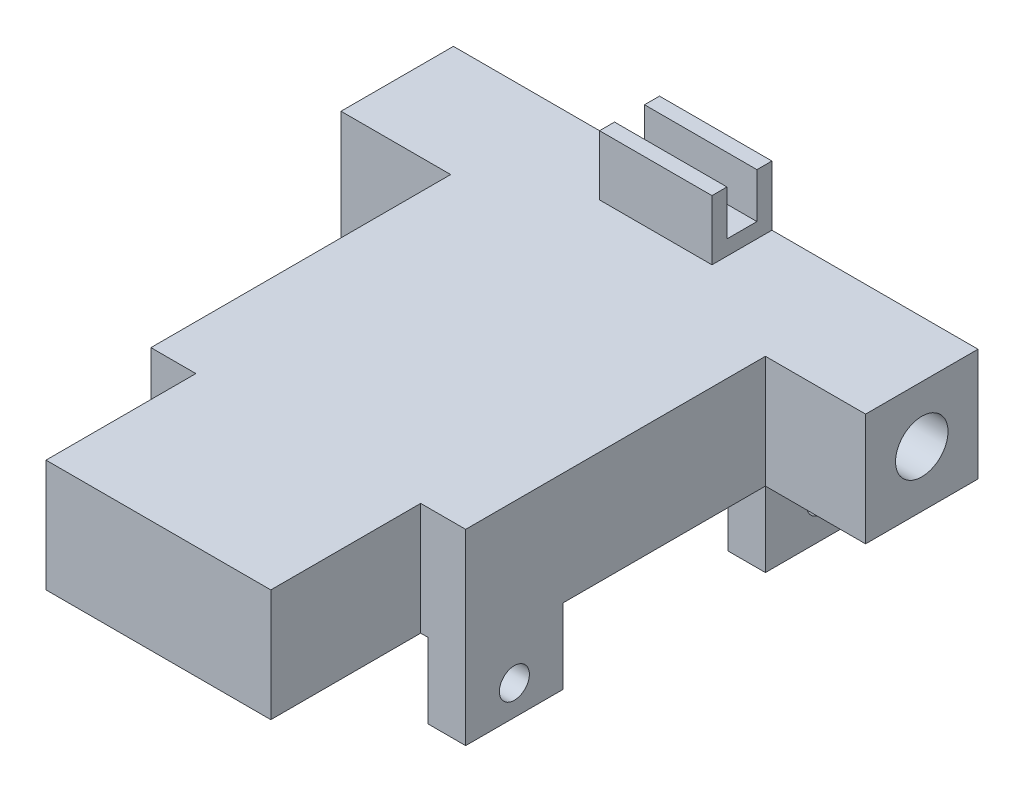
SolidWorks part; units mm, degrees
material "ABS"
ref_plane "Front Plane" through (0, 0, 0) normal (0, 0, 1) x (1, 0, 0)
ref_plane "Top Plane" through (0, 0, 0) normal (0, 1, 0) x (1, 0, 0)
ref_plane "Right Plane" through (0, 0, 0) normal (1, 0, 0) x (0, 0, -1)
sketch "Sketch1" plane through (0, 0, 0) normal (0, 0, 1) x (1, 0, 0)
  line L1 (0, 0) -> (88.9, 0)
  line L2 (0, 0) -> (0, -19.05)
  line L3 (0, -19.05) -> (88.9, -19.05)
  line L4 (88.9, 0) -> (88.9, -19.05)
  dimension "D1" = 88.9
  dimension "D2" = 19.05
extrude "Boss-Extrude1" add sketch "Sketch1" along normal blind 19.05
sketch "Sketch2" plane through (0, -19.05, 0) normal (0, -1, 0) x (1, 0, 0)
  line L0 (0, 19.05) -> (88.9, 19.05) construction
  line L1 (18.5839, 19.05) -> (24.9339, 19.05)
  line L2 (18.5839, 19.05) -> (18.5839, 0)
  line L3 (18.5839, 0) -> (24.9339, 0)
  line L4 (24.9339, 19.05) -> (24.9339, 0)
  line L5 (0, 0) -> (88.9, 0) construction
  line L7 (65.5739, 19.05) -> (71.9239, 19.05)
  line L8 (65.5739, 19.05) -> (65.5739, 0)
  line L9 (65.5739, 0) -> (71.9239, 0)
  line L10 (71.9239, 19.05) -> (71.9239, 0)
  point P12 (44.45, 0)
  dimension "D1" = 6.35
  dimension "D2" = 6.35
  dimension "D3" = 40.64
  dimension "D4" = 19.5161
extrude "Boss-Extrude2" add sketch "Sketch2" along normal blind 12.7
sketch "Sketch3" plane through (0, 0, 0) normal (-1, 0, 0) x (0, 0, 1)
  line L0 (0, 0) -> (0, -19.05) construction
  line L2 (19.05, -19.05) -> (0, -19.05) construction
  circle A0 centre (9.525, -9.525) radius 4.445
  dimension "D1" = 8.89
  dimension "D2" = 9.525
  dimension "D3" = 9.525
extrude "Cut-Extrude1" cut sketch "Sketch3" against normal blind 96.266
sketch "Sketch4" plane through (18.5839, 0, 0) normal (-1, 0, 0) x (0, 0, 1)
  line L0 (0, -31.75) -> (0, -19.05) construction
  line L1 (19.05, -31.75) -> (0, -31.75) construction
  circle A0 centre (9.525, -25.4) radius 2.54
  dimension "D1" = 5.08
  dimension "D2" = 9.525
  dimension "D3" = 6.35
extrude "Cut-Extrude2" cut sketch "Sketch4" against normal blind 96.266
sketch "Sketch5" plane through (0, 0, 19.05) normal (0, 0, 1) x (1, 0, 0)
  line L0 (88.9, 0) -> (0, 0) construction
  line L1 (18.5839, 0) -> (71.9239, 0)
  line L2 (18.5839, 0) -> (18.5839, -19.05)
  line L3 (18.5839, -19.05) -> (71.9239, -19.05)
  line L4 (71.9239, 0) -> (71.9239, -19.05)
  line L5 (71.9239, -19.05) -> (88.9, -19.05) construction
  line L6 (24.9339, -31.75) -> (24.9339, -19.05) construction
  dimension "D1" = 53.34
  dimension "D2" = 6.35
extrude "Boss-Extrude3" add sketch "Sketch5" along normal blind 50.8
sketch "Sketch6" plane through (0, -19.05, 0) normal (0, -1, 0) x (1, 0, 0)
  line L1 (18.5839, 69.85) -> (24.9339, 69.85)
  line L2 (18.5839, 69.85) -> (18.5839, 53.34)
  line L3 (18.5839, 53.34) -> (24.9339, 53.34)
  line L4 (24.9339, 69.85) -> (24.9339, 53.34)
  line L5 (71.9239, 69.85) -> (65.5739, 69.85)
  line L6 (71.9239, 69.85) -> (71.9239, 53.34)
  line L7 (71.9239, 53.34) -> (65.5739, 53.34)
  line L8 (65.5739, 69.85) -> (65.5739, 53.34)
  line L9 (18.5839, 69.85) -> (71.9239, 69.85) construction
  dimension "D1" = 6.35
  dimension "D2" = 6.35
  dimension "D3" = 16.51
  dimension "D4" = 16.51
extrude "Boss-Extrude4" add sketch "Sketch6" along normal blind 12.7
sketch "Sketch7" plane through (18.5839, 0, 0) normal (-1, 0, 0) x (0, 0, 1)
  line L0 (69.85, -31.75) -> (53.34, -31.75) construction
  line L1 (53.34, -31.75) -> (53.34, -19.05) construction
  circle A0 centre (61.595, -26.67) radius 2.54
  dimension "D1" = 5.08
  dimension "D2" = 5.08
  dimension "D3" = 8.255
extrude "Cut-Extrude3" cut sketch "Sketch7" against normal blind 61.976
sketch "Sketch8" plane through (0, 0, 0) normal (0, 1, 0) x (1, 0, 0)
  line L0 (88.9, 0) -> (0, 0) construction
  line L1 (34.925, 0) -> (53.975, 0)
  line L2 (34.925, 0) -> (34.925, -10.16)
  line L3 (34.925, -10.16) -> (53.975, -10.16)
  line L4 (53.975, 0) -> (53.975, -10.16)
  line L7 (88.9, 0) -> (0, 0)
  point P6 (44.45, 0)
  point P9 (44.45, 0)
  line M7 (88.9, 0) -> (0, 0)
  dimension "D1" = 19.05
  dimension "D2" = 10.16
extrude "Boss-Extrude5" add sketch "Sketch8" along normal blind 2.54 contours L4 L2 L3 M7
sketch "Sketch9" plane through (0, 2.54, 0) normal (0, 1, 0) x (1, 0, 0)
  line L0 (53.975, 0) -> (53.975, -10.16) construction
  line L1 (34.925, 0) -> (53.975, 0)
  line L2 (34.925, 0) -> (34.925, -2.54)
  line L3 (34.925, -2.54) -> (53.975, -2.54)
  line L4 (53.975, 0) -> (53.975, -2.54)
  line L6 (34.925, -10.16) -> (53.975, -10.16)
  line L7 (34.925, -10.16) -> (34.925, -7.62)
  line L8 (34.925, -7.62) -> (53.975, -7.62)
  line L9 (53.975, -10.16) -> (53.975, -7.62)
  dimension "D1" = 2.54
  dimension "D2" = 2.54
extrude "Boss-Extrude6" add sketch "Sketch9" along normal blind 7.62 contours L2 L1 L4 L3 | L7 L6 L9 L8
sketch "Sketch10" plane through (0, 0, 69.85) normal (0, 0, 1) x (1, 0, 0)
  line L0 (71.9239, 0) -> (18.5839, 0) construction
  line L1 (26.2039, 0) -> (64.3039, 0)
  line L2 (26.2039, 0) -> (26.2039, -19.05)
  line L3 (26.2039, -19.05) -> (64.3039, -19.05)
  line L4 (64.3039, 0) -> (64.3039, -19.05)
  line L5 (24.9339, -19.05) -> (65.5739, -19.05) construction
  point P8 (45.2539, -19.05)
  point P9 (45.2539, -19.05)
  point P10 (45.2539, 0)
  dimension "D1" = 19.05
extrude "Boss-Extrude7" add sketch "Sketch10" along normal blind 25.4
sketch "Sketch11" plane through (26.2039, 0, 0) normal (-1, 0, 0) x (0, 0, 1)
  line L0 (95.25, 0) -> (69.85, 0) construction
  line L1 (82.55, 0) -> (82.55, -19.05) construction
  line L2 (95.25, -9.525) -> (105.0469, -9.525) construction
  line L3 (95.25, 0) -> (95.25, -19.05) construction
  circle A0 centre (82.55, -9.525) radius 6.35
  dimension "D1" = 12.7
extrude "Cut-Extrude4" cut sketch "Sketch11" against normal blind 12.7
